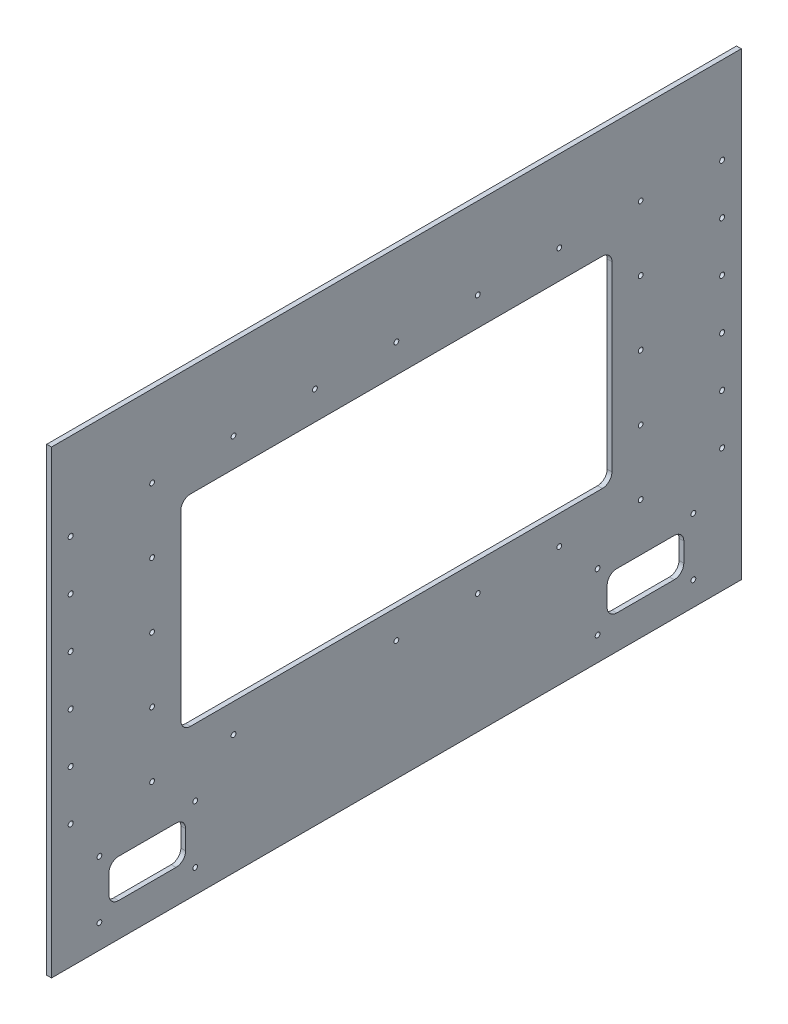
SolidWorks part; units mm, degrees
material "6061 Alloy"
ref_plane "Front Plane" through (0, 0, 0) normal (0, 0, 1) x (1, 0, 0)
ref_plane "Top Plane" through (0, 0, 0) normal (0, 1, 0) x (1, 0, 0)
ref_plane "Right Plane" through (0, 0, 0) normal (1, 0, 0) x (0, 0, -1)
sketch "Sketch1" plane through (-304.8, 0, 0) normal (-1, 0, 0) x (0, 0, 1)
  line L1 (-457.2, 0) -> (457.2, 0)
  line L2 (-457.2, 0) -> (-457.2, 609.6)
  line L3 (-457.2, 609.6) -> (457.2, 609.6)
  line L4 (457.2, 0) -> (457.2, 609.6)
  dimension "D1" = 609.6
extrude "Boss-Extrude1" add sketch "Sketch1" along normal blind 6.35 separate body
sketch "Sketch2" plane through (-311.15, 0, 0) normal (-1, 0, 0) x (0, 0, 1)
  line L0 (457.2, 609.6) -> (-457.2, 609.6) construction
  line L1 (-285.75, 463.55) -> (285.75, 463.55)
  line L2 (-285.75, 463.55) -> (-285.75, 196.85)
  line L3 (-285.75, 196.85) -> (285.75, 196.85)
  line L4 (285.75, 463.55) -> (285.75, 196.85)
  line L6 (-457.2, 609.6) -> (-457.2, 0) construction
  point P6 (0, 609.6)
  point P7 (0, 463.55)
  point P11 (-457.2, 304.8)
  dimension "D1" = 571.5
  dimension "D2" = 266.7
  dimension "D3" = 107.95
extrude "Cut-Extrude1" cut sketch "Sketch2" against normal through all
sketch "Sketch3" plane through (-311.15, 0, 0) normal (-1, 0, 0) x (0, 0, 1)
  line L0 (-457.2, 609.6) -> (-457.2, 0) construction
  line L1 (-381, 95.25) -> (-279.4, 95.25)
  line L2 (-381, 95.25) -> (-381, 44.45)
  line L3 (-381, 44.45) -> (-279.4, 44.45)
  line L4 (-279.4, 95.25) -> (-279.4, 44.45)
  line L6 (-279.4, 95.25) -> (-279.4, 139.7) construction
  line L7 (-327.66, 139.7) -> (327.66, 139.7) construction
  line L8 (-279.4, 44.45) -> (-279.4, 6.35) construction
  line L10 (-457.2, 0) -> (457.2, 0) construction
  line L11 (-393.7, 107.95) -> (-266.7, 107.95) construction
  line L12 (-393.7, 107.95) -> (-393.7, 31.75) construction
  line L13 (0, 0) -> (0, 264.8995) construction
  line L14 (279.4, 95.25) -> (279.4, 44.45)
  line L15 (381, 44.45) -> (279.4, 44.45)
  line L16 (381, 95.25) -> (279.4, 95.25)
  line L17 (381, 95.25) -> (381, 44.45)
  circle A0 centre (-393.7, 107.95) radius 12.7 construction
  circle A1 centre (-266.7, 107.95) radius 12.7 construction
  circle A2 centre (-266.7, 31.75) radius 12.7 construction
  circle A3 centre (-393.7, 31.75) radius 12.7 construction
  point P20 (-330.2, 107.95)
  point P21 (-330.2, 95.25)
  point P22 (-393.7, 69.85)
  point P23 (-381, 69.85)
  dimension "D7" = 25.4
  dimension "D1" = 50.8
  dimension "D2" = 101.6
  dimension "D3" = 76.2
  dimension "D4" = 6.35
  dimension "D5" = 38.1
  dimension "D6" = 44.45
  dimension "D8" = 12.7
  dimension "D9" = 12.7
extrude "Cut-Extrude2" cut sketch "Sketch3" against normal through all
fillet "Fillet1" radius 12.7 12 edges at (-307.975, 463.55, -285.75) (-307.975, 463.55, 285.75) (-307.975, 196.85, -285.75) (-307.975, 196.85, 285.75) (-307.975, 44.45, -279.4) (-307.975, 95.25, -279.4) (-307.975, 95.25, -381) (-307.975, 44.45, -381) (-307.975, 44.45, 381) (-307.975, 95.25, 381) (-307.975, 95.25, 279.4) (-307.975, 44.45, 279.4)
sketch "Sketch4" plane through (-311.15, 0, 0) normal (-1, 0, 0) x (0, 0, 1)
  circle A0 centre (-107.95, 158.75) radius 3.175 construction
  circle A1 centre (0, 158.75) radius 3.175 construction
  circle A2 centre (215.9, 158.75) radius 3.175 construction
  circle A3 centre (323.85, 158.75) radius 3.175 construction
  circle A13 centre (323.85, 244.475) radius 3.175 construction
  circle A14 centre (-323.85, 244.475) radius 3.175 construction
  circle A16 centre (323.85, 244.475) radius 3.175
  circle A17 centre (-323.85, 244.475) radius 3.175
  circle A22 centre (-107.95, 158.75) radius 3.175
  circle A23 centre (0, 158.75) radius 3.175
  circle A24 centre (215.9, 158.75) radius 3.175
  circle A25 centre (323.85, 158.75) radius 3.175
  circle A39 centre (-323.85, 158.75) radius 3.175 construction
  circle A40 centre (-215.9, 158.75) radius 3.175 construction
  circle A44 centre (-323.85, 158.75) radius 3.175
  circle A45 centre (-215.9, 158.75) radius 3.175
  circle A46 centre (266.7, 31.75) radius 3.175 construction
  circle A47 centre (393.7, 31.75) radius 3.175 construction
  circle A48 centre (266.7, 107.95) radius 3.175 construction
  circle A49 centre (393.7, 107.95) radius 3.175 construction
  circle A50 centre (-266.7, 31.75) radius 3.175 construction
  circle A51 centre (-393.7, 31.75) radius 3.175 construction
  circle A52 centre (-393.7, 107.95) radius 3.175 construction
  circle A53 centre (-266.7, 107.95) radius 3.175 construction
  circle A54 centre (266.7, 31.75) radius 3.175
  circle A55 centre (393.7, 31.75) radius 3.175
  circle A56 centre (266.7, 107.95) radius 3.175
  circle A57 centre (393.7, 107.95) radius 3.175
  circle A58 centre (-266.7, 31.75) radius 3.175
  circle A59 centre (-393.7, 31.75) radius 3.175
  circle A60 centre (-393.7, 107.95) radius 3.175
  circle A61 centre (-266.7, 107.95) radius 3.175
  circle A62 centre (323.85, 330.2) radius 3.175 construction
  circle A63 centre (323.85, 415.925) radius 3.175 construction
  circle A64 centre (323.85, 501.65) radius 3.175 construction
  circle A65 centre (215.9, 501.65) radius 3.175 construction
  circle A66 centre (107.95, 501.65) radius 3.175 construction
  circle A67 centre (0, 501.65) radius 3.175 construction
  circle A68 centre (-107.95, 501.65) radius 3.175 construction
  circle A69 centre (-215.9, 501.65) radius 3.175 construction
  circle A70 centre (-323.85, 501.65) radius 3.175 construction
  circle A71 centre (-323.85, 415.925) radius 3.175 construction
  circle A72 centre (-323.85, 330.2) radius 3.175 construction
  circle A73 centre (323.85, 330.2) radius 3.175
  circle A74 centre (323.85, 415.925) radius 3.175
  circle A75 centre (323.85, 501.65) radius 3.175
  circle A76 centre (215.9, 501.65) radius 3.175
  circle A77 centre (107.95, 501.65) radius 3.175
  circle A78 centre (0, 501.65) radius 3.175
  circle A79 centre (-107.95, 501.65) radius 3.175
  circle A80 centre (-215.9, 501.65) radius 3.175
  circle A81 centre (-323.85, 501.65) radius 3.175
  circle A82 centre (-323.85, 415.925) radius 3.175
  circle A83 centre (-323.85, 330.2) radius 3.175
extrude "Cut-Extrude3" cut sketch "Sketch4" against normal through all
sketch "Sketch5" plane through (-311.15, 0, 0) normal (-1, 0, 0) x (0, 0, 1)
  line L1 (-457.2, 584.2) -> (-457.2, 577.596) construction
  line L2 (-457.2, 577.596) -> (-450.85, 577.596) construction
  line L3 (-450.85, 577.596) -> (-450.85, 584.2) construction
  line L12 (-457.2, 603.25) -> (-457.2, 584.2) construction
  line L13 (-450.85, 603.25) -> (-450.85, 584.2) construction
  line L14 (-457.2, 603.25) -> (-450.85, 603.25) construction
  line L15 (-457.2, 584.2) -> (-457.2, 577.596) construction
  line L16 (-457.2, 577.596) -> (-450.85, 577.596) construction
  line L17 (-450.85, 577.596) -> (-450.85, 584.2) construction
  line L18 (-457.2, 603.25) -> (-457.2, 584.2) construction
  line L19 (-450.85, 603.25) -> (-450.85, 584.2) construction
  line L20 (-457.2, 603.25) -> (-450.85, 603.25) construction
  line L21 (-450.85, 609.6) -> (-450.85, 571.5)
  line L22 (-450.85, 571.5) -> (-457.2, 571.5)
  line L23 (457.2, 609.6) -> (-457.2, 609.6) construction
  line L24 (457.2, 609.6) -> (-457.2, 609.6)
  line L25 (-457.2, 609.6) -> (-457.2, 0) construction
  line L26 (-457.2, 609.6) -> (-457.2, 0)
  line L27 (457.2, 0) -> (457.2, 609.6) construction
  line L28 (457.2, 0) -> (457.2, 609.6)
  line L29 (450.85, 609.6) -> (450.85, 571.5)
  line L30 (450.85, 571.5) -> (457.2, 571.5)
  dimension "D1" = 6.35
  dimension "D2" = 38.1
extrude "Cut-Extrude4" [suppressed] cut sketch "Sketch5" against normal through all contours L24 L26 L22 L21 | L29 L30 L28 L24
fillet "Fillet2" [suppressed] radius 6.604
sketch "Sketch6" plane through (-311.15, 0, 0) normal (-1, 0, 0) x (0, 0, 1)
  line L0 (431.8, 0) -> (431.8, 6.35) construction
  line L1 (-457.2, 0) -> (457.2, 0) construction
  line L2 (457.2, 0) -> (457.2, 609.6) construction
  line L3 (431.8, 6.35) -> (431.8, 164.084) construction
  circle A0 centre (431.8, 164.084) radius 3.302
  circle A1 centre (431.8, 230.124) radius 3.302
  circle A2 centre (431.8, 296.164) radius 3.302
  circle A3 centre (431.8, 362.204) radius 3.302
  circle A4 centre (431.8, 428.244) radius 3.302
  circle A5 centre (431.8, 494.284) radius 3.302
  circle A6 centre (-431.8, 230.124) radius 3.302
  circle A7 centre (-431.8, 296.164) radius 3.302
  circle A8 centre (-431.8, 362.204) radius 3.302
  circle A9 centre (-431.8, 428.244) radius 3.302
  circle A10 centre (-431.8, 494.284) radius 3.302
  circle A11 centre (-431.8, 164.084) radius 3.302
  dimension "D4" = 6.604
  dimension "D1" = 6.35
  dimension "D2" = 25.4
  dimension "D3" = 157.734
  dimension "D5" = 6
  dimension "D6" = 2
extrude "Cut-Extrude5" cut sketch "Sketch6" against normal up to surface (6.35 mm away) up to face at (-304.8, 107.95, 396.875)
equation "\"D3@Sketch2\"=(\"D2@Sketch2\"/2)-1"
equation "\"D9@Sketch3\"=\"D8@Sketch3\""
